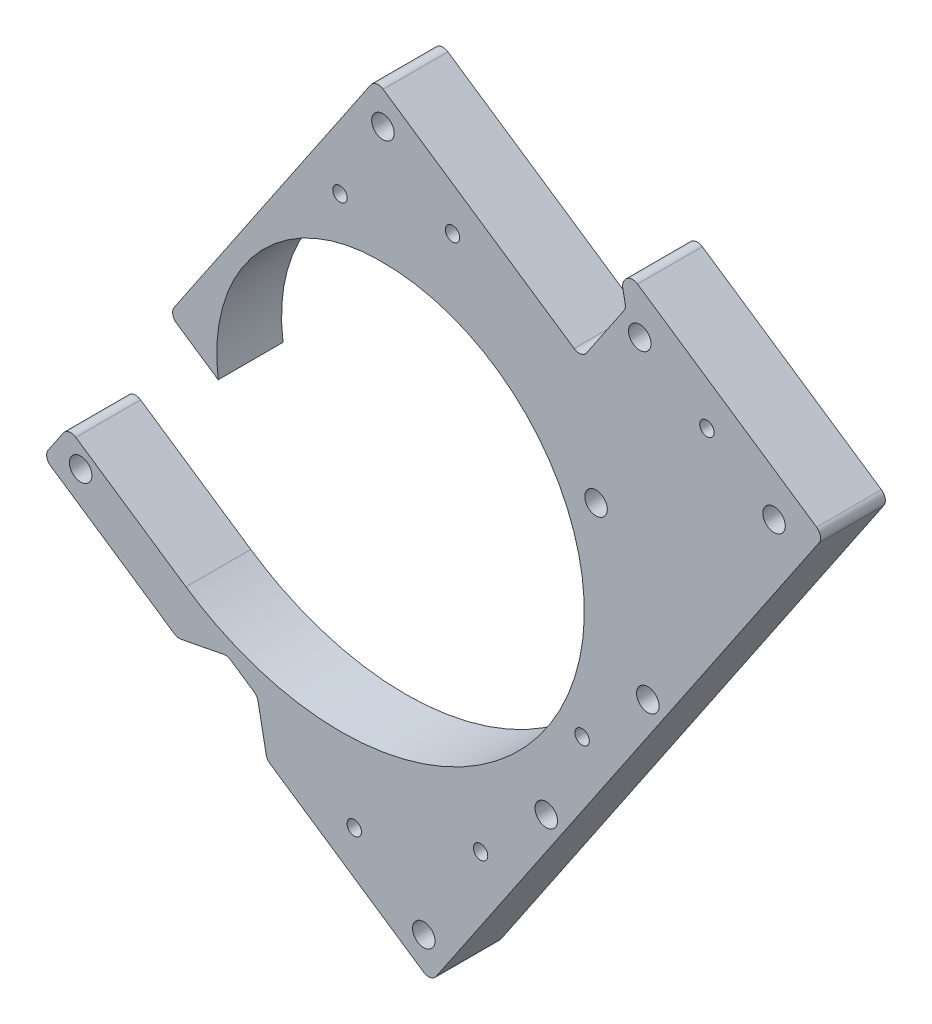
SolidWorks part; units mm, degrees
ref_plane "Front Plane" through (0, 0, 0) normal (0, 0, 1) x (1, 0, 0)
ref_plane "Top Plane" through (0, 0, 0) normal (0, 1, 0) x (1, 0, 0)
ref_plane "Right Plane" through (0, 0, 0) normal (1, 0, 0) x (0, 0, -1)
sketch "Sketch1" plane through (0, 0, 0) normal (0, 0, 1) x (1, 0, 0)
  line L0 (0, 31.75) -> (0, 57.15) construction
  line L1 (31.75, 0) -> (67.31, 0) construction
  line L3 (0, -31.75) -> (0, -97.79) construction
  line L4 (22.4506, -22.4506) -> (58.3717, -58.3717) construction
  line L5 (-22.4506, -22.4506) -> (-72.7401, -72.7401) construction
  line L6 (57.493, 23.8144) -> (29.3332, 12.1502) construction
  line L7 (-40.4112, 40.4112) -> (-22.4506, 22.4506) construction
  line L8 (42.2072, 42.2072) -> (22.4506, 22.4506) construction
  line L9 (71.5729, -29.6465) -> (29.3332, -12.1502) construction
  line L10 (33.5345, -80.9596) -> (12.1502, -29.3332) construction
  line L11 (-37.4226, -90.3462) -> (-12.1502, -29.3332) construction
  circle A0 centre (0, 0) radius 31.75 construction
  circle A3 centre (0, 0) radius 50.8 construction
  dimension "D4" = 63.5
  dimension "D24" = 101.6
  dimension "D2" = 25.4
  dimension "D3" = 35.56
  dimension "D5" = 66.04
  dimension "D6" = 45
  dimension "D7" = 50.8
  dimension "D8" = 71.12
  dimension "D9" = 45
  dimension "D10" = 45
  dimension "D11" = 27.94
  dimension "D12" = 45
  dimension "D13" = 22.5
  dimension "D14" = 22.5
  dimension "D15" = 22.5
  dimension "D16" = 25.4
  dimension "D17" = 45.72
  dimension "D18" = 55.88
  dimension "D19" = 66.04
  dimension "D20" = 22.5
  dimension "D21" = 30.48
sketch "Sketch6" plane through (0, 0, 0) normal (0, 0, 1) x (1, 0, 0)
  line L0 (0, 0) -> (0, 57.15) construction
  line L1 (-68.0069, -76.6709) -> (-109.4868, -48.6565)
  line L2 (-109.4868, -48.6565) -> (-73.9468, 3.9663) construction
  line L3 (-73.9468, 3.9663) -> (-56.6244, -7.7327)
  line L4 (-73.9468, 3.9663) -> (-1.0899, 111.8431)
  line L5 (-1.0899, 111.8431) -> (135.7295, 19.4391)
  line L6 (135.7295, 19.4391) -> (18.4476, -154.2162)
  line L7 (18.4476, -154.2162) -> (-118.3718, -61.8122)
  line L8 (-118.3718, -61.8122) -> (-109.4868, -48.6565)
  arc A0 (0, 57.15) -> (-56.6244, -7.7327) centre (0, 0) ccw
  arc A1 (0, 57.15) -> (70.8293, -29.3385) centre (1.3636, -13.9802) cw
  spline S0 degree 4 poles (72.5802, -14.4204) (72.5732, -14.8939) (72.5509, -15.8408) (72.5026, -17.0238) (72.4142, -18.4418) (72.3202, -19.622) (72.2329, -20.5651) (72.1094, -21.7358) (71.9666, -22.9009) (71.8046, -24.0602) (71.6239, -25.2132) (71.4679, -26.1331) (71.3203, -26.9417) (71.191, -27.6137) (71.0723, -28.2005) (70.9682, -28.6984) (70.8717, -29.1472) (70.8012, -29.4669) (70.7133, -29.8548) (70.619, -30.2629) (70.5011, -30.7621) (70.364, -31.3222) (70.1993, -31.971) (70.0005, -32.7239) (69.7951, -33.4698) (69.582, -34.2143) (69.3614, -34.9567) (69.1333, -35.6968) (68.8388, -36.6189) (68.4706, -37.7207) (68.0195, -38.9988) (67.4748, -40.4488) (66.9013, -41.8877) (66.2993, -43.3149) (65.6691, -44.7298) (65.0111, -46.132) (64.3256, -47.521) (63.613, -48.8963) (62.8736, -50.2574) (62.1078, -51.6038) (61.3159, -52.935) (60.4985, -54.2507) (59.6557, -55.5503) (58.5712, -57.1543) (57.221, -59.0453) (55.576, -61.2004) (53.604, -63.5903) (51.5433, -65.9041) (49.3973, -68.139) (47.1695, -70.2924) (44.8635, -72.3618) (42.4828, -74.3448) (40.0312, -76.2394) (36.8825, -78.4946) (32.9768, -81.016) (28.2508, -83.6809) (21.4155, -86.9191) (14.3083, -89.5267) (6.997, -91.4882) (-0.4519, -92.7974) (-6.6169, -93.4564) (-12.812, -93.702) (-19.0096, -93.5373) (-25.1831, -92.9667) (-31.3064, -91.9964) (-36.5985, -90.8043) (-41.0725, -89.5432) (-44.7523, -88.3359) (-47.6642, -87.2776) (-50.5413, -86.1284) (-53.3811, -84.8896) (-56.1809, -83.563) (-58.5935, -82.3267) (-60.6334, -81.2142) (-62.3138, -80.2525) (-63.6461, -79.4625) (-64.9661, -78.6522) (-66.2736, -77.8217) (-67.4063, -77.0777) (-68.3692, -76.4276) (-69.1659, -75.8779) (-69.7996, -75.4335) (-70.4313, -74.9832) (-71.06, -74.5278) (-71.6725, -74.0775) (-72.2987, -73.6093) (-72.9683, -73.0996) (-73.347, -72.808) (-73.9663, -72.325) (-74.6801, -71.7609) (-75.4046, -71.175) (-76.2838, -70.4507) (-77.1319, -69.735) (-77.9818, -69.0025) (-78.8195, -68.2643) (-79.6511, -67.5155) (-80.4737, -66.7585) (-81.4921, -65.8008) (-82.6974, -64.6343) (-83.8818, -63.4463) (-85.0447, -62.2374) (-85.8084, -61.4205) (-86.1873, -61.0093) (-86.376, -60.8031) knots 0 0 0 0 0 0.008941 0.017882 0.022352 0.026823 0.031293 0.035764 0.044578 0.048985 0.053392 0.057799 0.062207 0.06441 0.066614 0.068817 0.071021 0.072848 0.074676 0.076504 0.078332 0.081987 0.085642 0.089298 0.092953 0.096609 0.100264 0.103919 0.107575 0.114886 0.122197 0.129507 0.136818 0.144129 0.15144 0.158751 0.166062 0.173372 0.180683 0.187994 0.195305 0.202616 0.209927 0.217237 0.231859 0.246481 0.261102 0.275724 0.290346 0.304967 0.319589 0.334211 0.348832 0.363454 0.392697 0.421941 0.451184 0.506141 0.535384 0.564627 0.593871 0.623114 0.652357 0.681601 0.710844 0.740087 0.754709 0.769331 0.783952 0.798574 0.813196 0.827817 0.842439 0.84975 0.857061 0.864371 0.871682 0.878993 0.886304 0.889959 0.893615 0.89727 0.900926 0.904581 0.908237 0.911892 0.915547 0.918186 0.920826 0.926104 0.931382 0.936661 0.941939 0.947217 0.952495 0.957774 0.963052 0.96833 0.978887 0.989443 0.994722 1 1 1 1 1 construction
  spline S1 degree 4 poles (70.8293, -29.3385) (70.8117, -29.4183) (70.776, -29.5781) (70.7133, -29.8548) (70.619, -30.2629) (70.5011, -30.7621) (70.364, -31.3222) (70.1993, -31.971) (70.0005, -32.7239) (69.7951, -33.4698) (69.582, -34.2143) (69.3614, -34.9567) (69.1333, -35.6968) (68.8388, -36.6189) (68.4706, -37.7207) (68.0195, -38.9988) (67.4748, -40.4488) (66.9013, -41.8877) (66.2993, -43.3149) (65.6691, -44.7298) (65.0111, -46.132) (64.3256, -47.521) (63.613, -48.8963) (62.8736, -50.2574) (62.1078, -51.6038) (61.3159, -52.935) (60.4985, -54.2507) (59.6557, -55.5503) (58.5712, -57.1543) (57.221, -59.0453) (55.576, -61.2004) (53.604, -63.5903) (51.5433, -65.9041) (49.3973, -68.139) (47.1695, -70.2924) (44.8635, -72.3618) (42.4828, -74.3448) (40.0312, -76.2394) (36.8825, -78.4946) (32.9768, -81.016) (28.2508, -83.6809) (21.4155, -86.9191) (14.3083, -89.5267) (6.997, -91.4882) (-0.4519, -92.7974) (-6.6169, -93.4564) (-12.812, -93.702) (-19.0096, -93.5373) (-25.1831, -92.9667) (-31.3064, -91.9964) (-36.5985, -90.8043) (-41.0725, -89.5432) (-44.7523, -88.3359) (-47.6642, -87.2776) (-50.5413, -86.1284) (-53.3811, -84.8896) (-56.1809, -83.563) (-58.5935, -82.3267) (-60.6334, -81.2142) (-62.3138, -80.2525) (-63.6461, -79.4625) (-64.9661, -78.6522) (-66.2224, -77.8543) (-67.143, -77.2506) (-67.7363, -76.8537) (-68.0069, -76.6709) knots 0.071021 0.071021 0.071021 0.071021 0.071021 0.072848 0.074676 0.076504 0.078332 0.081987 0.085642 0.089298 0.092953 0.096609 0.100264 0.103919 0.107575 0.114886 0.122197 0.129507 0.136818 0.144129 0.15144 0.158751 0.166062 0.173372 0.180683 0.187994 0.195305 0.202616 0.209927 0.217237 0.231859 0.246481 0.261102 0.275724 0.290346 0.304967 0.319589 0.334211 0.348832 0.363454 0.392697 0.421941 0.451184 0.506141 0.535384 0.564627 0.593871 0.623114 0.652357 0.681601 0.710844 0.740087 0.754709 0.769331 0.783952 0.798574 0.813196 0.827817 0.842439 0.84975 0.857061 0.864371 0.871682 0.878993 0.885158 0.885158 0.885158 0.885158 0.885158
  dimension "D1" = 57.15
  dimension "D2" = 101.6
  dimension "D3" = 63.5
  dimension "D4" = 63.5
  dimension "D5" = 15.875
  dimension "D6" = 101.6
  dimension "D7" = 209.55
extrude "Boss-Extrude2" add sketch "Sketch6" along normal blind 22.86
sketch "Sketch8" plane through (0, 0, 22.86) normal (0, 0, 1) x (1, 0, 0)
  line L0 (-71.0112, -93.7982) -> (-53.3787, -90.3816)
  line L1 (-118.3718, -61.8122) -> (18.4476, -154.2162) construction
  line L2 (-53.3787, -90.3816) -> (-42.8541, -97.4896)
  line L3 (-42.8541, -97.4896) -> (-39.4375, -115.1222)
  line L4 (-39.4375, -115.1222) -> (-71.0112, -93.7982)
  line L5 (18.4476, -154.2162) -> (135.7295, 19.4391) construction
  dimension "D1" = 82.55
  dimension "D2" = 12.7
  dimension "D3" = 12.7
  dimension "D4" = 45
  dimension "D5" = 45
extrude "Cut-Extrude1" cut sketch "Sketch8" against normal through all
sketch "Sketch9" plane through (0, 0, 22.86) normal (0, 0, 1) x (1, 0, 0)
  line L0 (-1.0899, 111.8431) -> (-109.4868, -48.6565)
  line L1 (-1.0899, 111.8431) -> (135.7295, 19.4391)
  line L2 (-109.4868, -48.6565) -> (27.3325, -141.0605)
  line L3 (135.7295, 19.4391) -> (27.3325, -141.0605)
  line L4 (18.4476, -154.2162) -> (135.7295, 19.4391) construction
sketch "Sketch10" plane through (0, 0, 22.86) normal (0, 0, 1) x (1, 0, 0)
  line L0 (76.6361, 21.2777) -> (4.9965, -84.7966) construction
  line L2 (-39.4375, -115.1222) -> (18.4476, -154.2162) construction
  line L3 (0, 0) -> (-45.2952, -45.2145) construction
  line L4 (-45.2952, -45.2145) -> (4.9965, -84.7966) construction
  line L5 (18.4476, -154.2162) -> (135.7295, 19.4391) construction
  circle A0 centre (4.9965, -84.7966) radius 3.9688
  circle A1 centre (40.8163, -31.7595) radius 3.9687
  circle A2 centre (76.6361, 21.2777) radius 3.9687
  circle A3 centre (-45.2952, -45.2145) radius 3.9687
  dimension "D1" = 7.9375
  dimension "D2" = 50
  dimension "D3" = 50
  dimension "D4" = 128
  dimension "D5" = 64
extrude "Cut-Extrude2" cut sketch "Sketch10" against normal through all
sketch "Sketch12" plane through (0, 0, 22.86) normal (0, 0, 1) x (1, 0, 0)
  line L0 (135.7295, 19.4391) -> (67.3198, 65.6411)
  line L1 (135.7295, 19.4391) -> (157.0534, 51.0128)
  line L2 (67.3198, 65.6411) -> (88.6438, 97.2148)
  line L3 (157.0534, 51.0128) -> (88.6438, 97.2148)
  line L4 (135.7295, 19.4391) -> (-1.0899, 111.8431) construction
  dimension "D1" = 82.55
  dimension "D2" = 38.1
extrude "Boss-Extrude4" add sketch "Sketch12" against normal through all
sketch "Sketch13" plane through (0, 0, 22.86) normal (0, 0, 1) x (1, 0, 0)
  line L0 (40.8163, -31.7595) -> (76.6361, 21.2777) construction
  line L1 (18.4476, -154.2162) -> (157.0534, 51.0128) construction
  line L2 (58.7262, -5.2409) -> (94.8992, -29.6711) construction
  circle A0 centre (94.8992, -29.6711) radius 3.9687
  dimension "D1" = 7.9375
  dimension "D2" = 6.35
extrude "Cut-Extrude5" cut sketch "Sketch13" against normal through all
pattern_linear "LPattern1" count 2 spacing 64 along (-0.5597, -0.8287, 0) of "Cut-Extrude5"
sketch "Sketch14" plane through (0, 0, 22.86) normal (0, 0, 1) x (1, 0, 0)
  line L0 (59.0794, -82.7083) -> (94.8992, -29.6711) construction
  line L1 (76.9893, -56.1897) -> (71.727, -52.6357) construction
  line L2 (18.4476, -154.2162) -> (157.0534, 51.0128) construction
  line L3 (115.7406, 63.5892) -> (122.8486, 74.1138) construction
  line L4 (157.0534, 51.0128) -> (88.6438, 97.2148) construction
  circle A0 centre (71.727, -52.6357) radius 2.54
  circle A1 centre (35.9072, -105.6729) radius 2.54
  circle A2 centre (115.7406, 63.5892) radius 2.54
  dimension "D1" = 5.08
  dimension "D2" = 12.7
  dimension "D4" = 12.7
  dimension "D3" = 2
extrude "Cut-Extrude6" cut sketch "Sketch14" against normal through all
sketch "Sketch15" plane through (0, 0, 22.86) normal (0, 0, 1) x (1, 0, 0)
  line L0 (-118.3718, -61.8122) -> (-71.0112, -93.7982) construction
  line L1 (-39.4375, -115.1222) -> (18.4476, -154.2162) construction
  line L2 (18.4476, -154.2162) -> (157.0534, 51.0128) construction
  line L3 (-1.0899, 111.8431) -> (-73.9468, 3.9663) construction
  line L4 (67.3198, 65.6411) -> (-1.0899, 111.8431) construction
  circle A0 centre (-105.1473, -59.2498) radius 3.9687
  circle A1 centre (15.8851, -140.9917) radius 3.9687
  circle A2 centre (59.0794, -82.7083) radius 3.9687 construction
  circle A3 centre (1.4726, 98.6186) radius 3.9687
  dimension "D7" = 7.9375
  dimension "D1" = 9.525
  dimension "D2" = 9.525
  dimension "D3" = 9.525
  dimension "D4" = 9.525
  dimension "D5" = 9.525
  dimension "D6" = 9.525
extrude "Cut-Extrude7" cut sketch "Sketch15" against normal through all
sketch "Sketch16" plane through (0, 0, 22.86) normal (0, 0, 1) x (1, 0, 0)
  line L0 (157.0534, 51.0128) -> (88.6438, 97.2148) construction
  line L1 (88.6438, 97.2148) -> (67.3198, 65.6411) construction
  line L2 (18.4476, -154.2162) -> (157.0534, 51.0128) construction
  circle A0 centre (92.0604, 79.5822) radius 3.9687
  circle A1 centre (139.4209, 47.5962) radius 3.9687
  circle A2 centre (94.8992, -29.6711) radius 3.9687 construction
  dimension "D1" = 12.7
  dimension "D2" = 12.7
  dimension "D3" = 12.7
  dimension "D4" = 12.7
extrude "Cut-Extrude8" cut sketch "Sketch16" against normal through all
sketch "Sketch19" plane through (0, 0, 22.86) normal (0, 0, 1) x (1, 0, 0)
  line L0 (88.6438, 97.2148) -> (67.3198, 65.6411) construction
  line L1 (67.3198, 65.6411) -> (-1.0899, 111.8431) construction
  line L2 (18.4476, -154.2162) -> (-118.3718, -61.8122) construction
  line L3 (-65.6802, -85.9048) -> (35.6087, 64.0702) construction
  line L4 (-73.9468, 3.9663) -> (-1.0899, 111.8431) construction
  circle A0 centre (35.6087, 64.0702) radius 3.9687 construction
  circle A1 centre (-65.6802, -85.9048) radius 3.9687
  dimension "D1" = 7.9375
  dimension "D2" = 25.4
  dimension "D3" = 19.05
  dimension "D4" = 9.525
extrude "Cut-Extrude11" cut sketch "Sketch19" against normal through all
sketch "Sketch21" plane through (0, 0, 22.86) normal (0, 0, 1) x (1, 0, 0)
  line L0 (-73.9468, 3.9663) -> (-1.0899, 111.8431) construction
  line L1 (67.3198, 65.6411) -> (-1.0899, 111.8431) construction
  line L2 (-118.3718, -61.8122) -> (-71.0112, -93.7982) construction
  line L3 (-39.4375, -115.1222) -> (18.4476, -154.2162) construction
  line L5 (-8.6493, -120.5906) -> (115.7406, 63.5892) construction
  line L6 (18.4476, -154.2162) -> (157.0534, 51.0128) construction
  line L7 (-118.3718, -61.8122) -> (-109.4868, -48.6565) construction
  circle A0 centre (-13.6663, 70.5302) radius 2.54
  circle A1 centre (26.007, 78.2175) radius 2.54
  circle A2 centre (-86.7294, -71.6888) radius 2.54
  circle A3 centre (-8.6493, -120.5906) radius 2.54
  circle A4 centre (35.9072, -105.6729) radius 2.54 construction
  dimension "D1" = 12.7
  dimension "D2" = 12.7
  dimension "D3" = 9.525
  dimension "D4" = 12.7
  dimension "D5" = 41.275
  dimension "D6" = 31.75
  dimension "D7" = 41.275
extrude "Cut-Extrude12" cut sketch "Sketch21" against normal through all
sketch "Sketch23" plane through (0, 0, 22.86) normal (0, 0, 1) x (1, 0, 0)
  circle A0 centre (-65.6802, -85.9048) radius 4.1679
  circle A1 centre (-86.7294, -71.6888) radius 4.4404
extrude "Boss-Extrude5" add sketch "Sketch23" against normal through all
sketch "Sketch25" plane through (0, 0, 22.86) normal (0, 0, 1) x (1, 0, 0)
  line L0 (85.8006, 93.0049) -> (87.1672, 85.9519)
  line L1 (88.6438, 97.2148) -> (67.3198, 65.6411) construction
  line L2 (87.1672, 85.9519) -> (71.5296, 62.7979)
  line L3 (67.3198, 65.6411) -> (71.5296, 62.7979)
  line L4 (67.3198, 65.6411) -> (85.8006, 93.0049)
  line L5 (67.3198, 65.6411) -> (-1.0899, 111.8431) construction
  dimension "D1" = 45
  dimension "D3" = 5.08
  dimension "D4" = 5.08
extrude "Cut-Extrude13" cut sketch "Sketch25" against normal through all
fillet "Fillet1" radius 3.175 14 edges at (87.1672, 85.9519, 11.43) (85.8006, 93.0049, 11.43) (88.6438, 97.2148, 11.43) (-1.0899, 111.8431, 11.43) (-73.9468, 3.9663, 11.43) (-109.4868, -48.6565, 11.43) (-118.3718, -61.8122, 11.43) (-39.4375, -115.1222, 11.43) (-71.0112, -93.7982, 11.43) (18.4476, -154.2162, 11.43) (157.0534, 51.0128, 11.43) (71.5296, 62.7979, 11.43) (-42.8541, -97.4896, 11.43) (-53.3787, -90.3816, 11.43)
